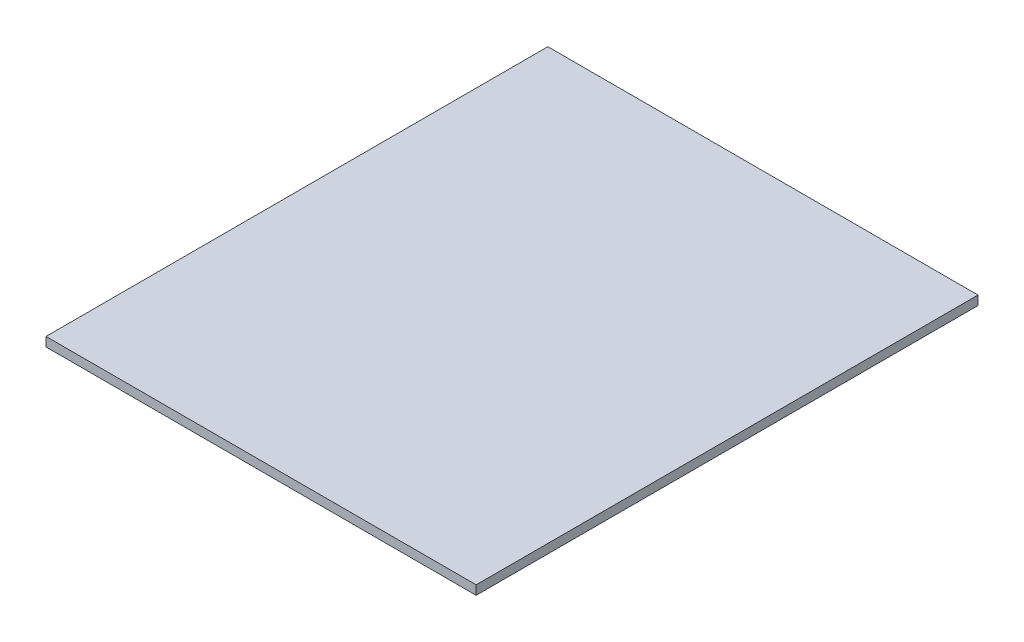
SolidWorks part; units mm, degrees
ref_plane "Alzado" through (0, 0, 0) normal (0, 0, 1) x (1, 0, 0)
ref_plane "Planta" through (0, 0, 0) normal (0, 1, 0) x (1, 0, 0)
ref_plane "Vista lateral" through (0, 0, 0) normal (1, 0, 0) x (0, 0, -1)
sketch "Croquis1" plane through (0, 0, 0) normal (0, 1, 0) x (1, 0, 0)
  line L1 (300, -350) -> (-300, -350)
  line L2 (300, -350) -> (300, 350)
  line L3 (300, 350) -> (-300, 350)
  line L4 (-300, -350) -> (-300, 350)
  line L5 (300, -350) -> (-300, 350) construction
  line L6 (300, 350) -> (-300, -350) construction
  point P0 (0, 0)
  dimension "D1" = 600
  dimension "D2" = 700
extrude "Saliente-Extruir1" add sketch "Croquis1" along normal blind 12.7
